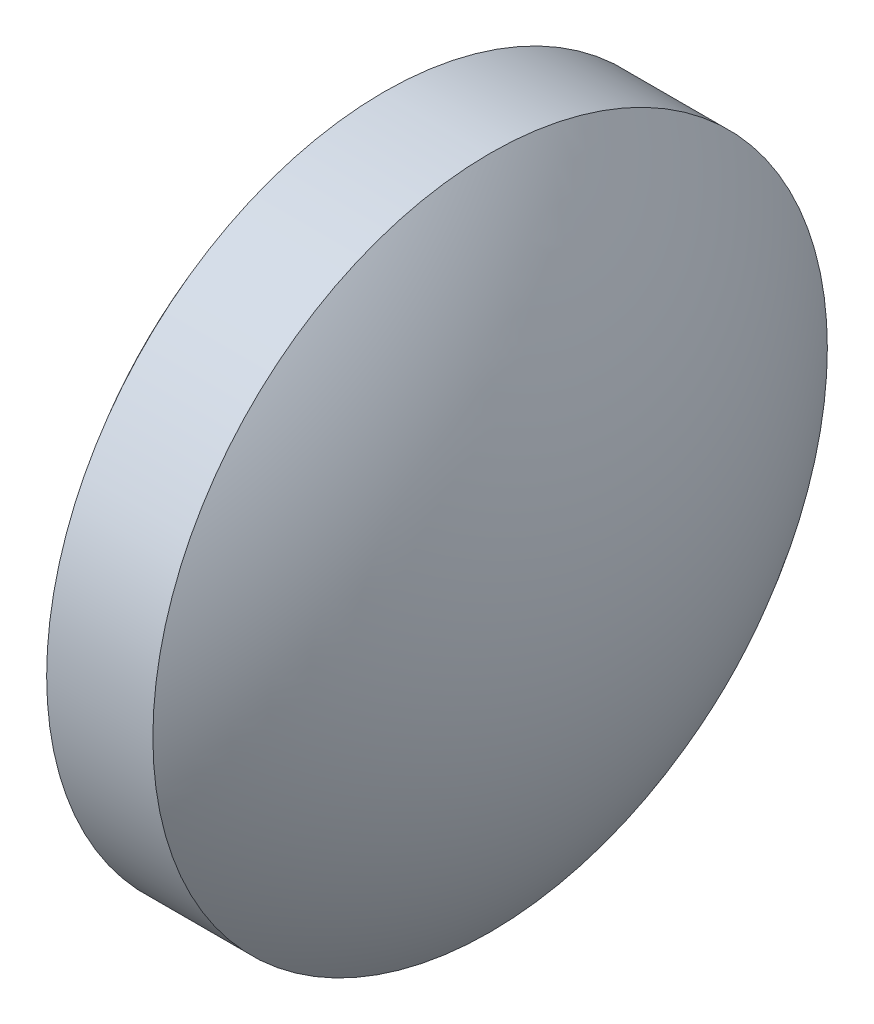
SolidWorks part; units mm, degrees
ref_plane "前视基准面" through (0, 0, 0) normal (0, 0, 1) x (1, 0, 0)
ref_plane "上视基准面" through (0, 0, 0) normal (0, 1, 0) x (1, 0, 0)
ref_plane "右视基准面" through (0, 0, 0) normal (1, 0, 0) x (0, 0, -1)
sketch "草图1" plane through (0, 0, 0) normal (0, 0, 1) x (1, 0, 0)
  line L0 (42.2291, 30.6581) -> (44.2291, 30.6581)
  line L1 (44.2291, 30.6581) -> (44.2291, 17.9581)
  line L2 (44.2291, 17.9581) -> (42.2291, 17.9581)
  line L3 (42.2291, 17.9581) -> (42.2291, 30.6581)
  line L4 (35.8268, 24.3081) -> (50.6314, 24.3081) construction
  arc A0 (42.2291, 30.6581) -> (42.2291, 17.9581) centre (50.6314, 24.3081) ccw
  arc A1 (44.2291, 17.9581) -> (44.2291, 30.6581) centre (35.8268, 24.3081) ccw
  dimension "D1" = 12.7
  dimension "D2" = 2.0001
revolve "旋转1" add sketch "草图1" angle 360 about L4
